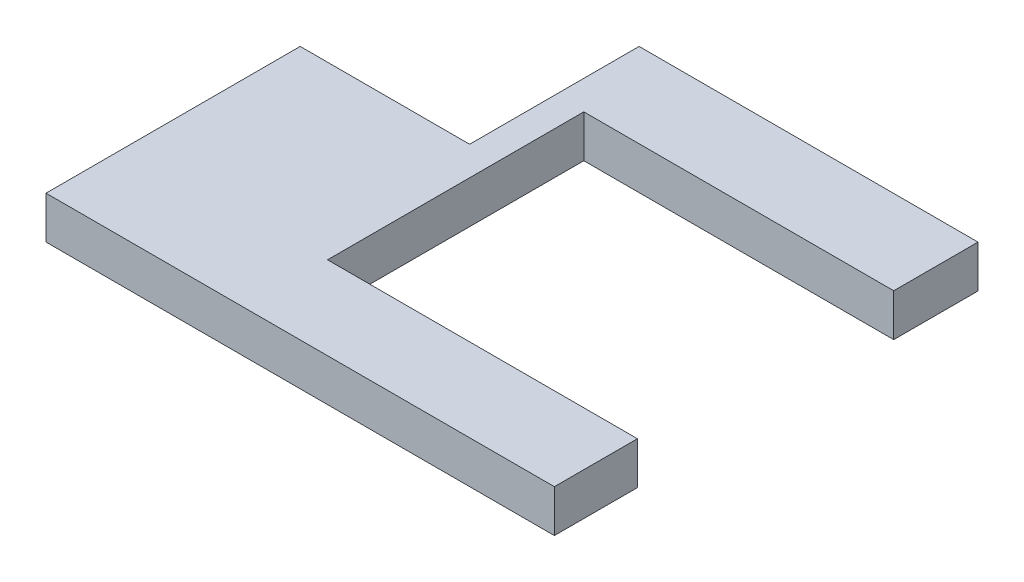
SolidWorks part; units mm, degrees
ref_plane "Спереди" through (0, 0, 0) normal (0, 0, 1) x (1, 0, 0)
ref_plane "Сверху" through (0, 0, 0) normal (0, 1, 0) x (1, 0, 0)
ref_plane "Справа" through (0, 0, 0) normal (1, 0, 0) x (0, 0, -1)
sketch "Эскиз1" plane through (0, 0, 0) normal (0, 1, 0) x (1, 0, 0)
  line L0 (0, 0) -> (120, 0)
  line L2 (120, 100) -> (40, 100)
  line L3 (40, 100) -> (40, 60)
  line L4 (40, 60) -> (0, 60)
  line L5 (0, 60) -> (0, 0)
  line L6 (120, 0) -> (120, 19.6053)
  line L7 (120, 19.6053) -> (46.8508, 19.6053)
  line L8 (46.8508, 19.6053) -> (46.8508, 80.1036)
  line L9 (46.8508, 80.1036) -> (120, 80.1036)
  line L10 (120, 80.1036) -> (120, 100)
extrude "Бобышка-Вытянуть1" add sketch "Эскиз1" along normal blind 10
